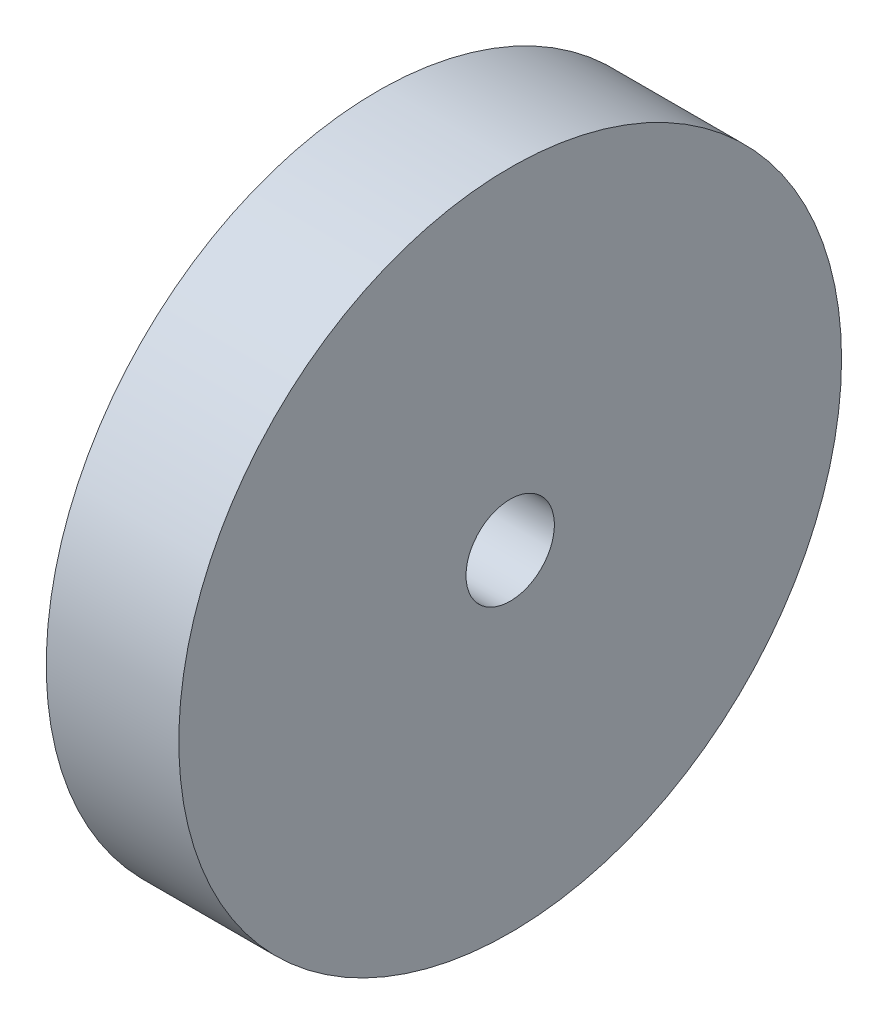
SolidWorks part; units mm, degrees
material "BUTYL"
ref_plane "Front Plane" through (0, 0, 0) normal (0, 0, 1) x (1, 0, 0)
ref_plane "Top Plane" through (0, 0, 0) normal (0, 1, 0) x (1, 0, 0)
ref_plane "Right Plane" through (0, 0, 0) normal (1, 0, 0) x (0, 0, -1)
sketch "Sketch2" plane through (0, 0, 0) normal (1, 0, 0) x (0, 0, -1)
  circle A0 centre (0, 0) radius 37.5
  dimension "D1" = 75
extrude "Boss-Extrude1" add sketch "Sketch2" along normal blind 15
sketch "Sketch4" plane through (0, 0, 0) normal (-1, 0, 0) x (0, 0, 1)
  circle A0 centre (0, 0) radius 5
  dimension "D1" = 10
extrude "Cut-Extrude1" cut sketch "Sketch4" against normal through all
